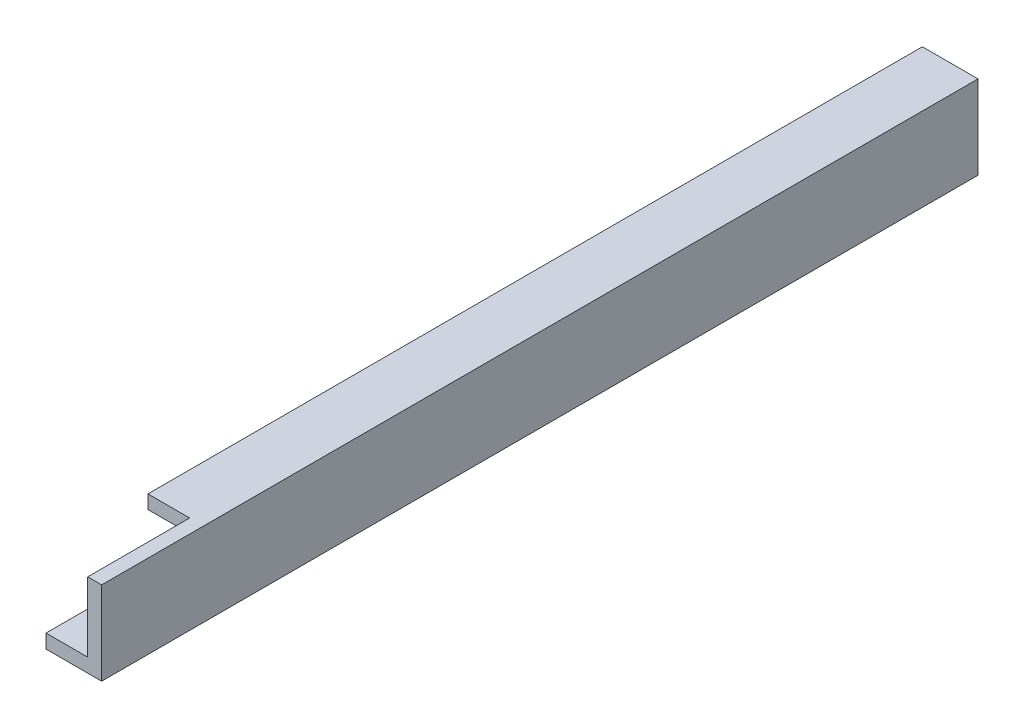
SolidWorks part; units mm, degrees
ref_plane "Front Plane" through (0, 0, 0) normal (0, 0, 1) x (1, 0, 0)
ref_plane "Top Plane" through (0, 0, 0) normal (0, 1, 0) x (1, 0, 0)
ref_plane "Right Plane" through (0, 0, 0) normal (1, 0, 0) x (0, 0, -1)
sketch "Sketch2" plane through (0, 0, 0) normal (0, 1, 0) x (1, 0, 0)
  line L1 (0, 0) -> (25.4, 0)
  line L2 (0, 0) -> (0, 400.05)
  line L3 (0, 400.05) -> (25.4, 400.05)
  line L4 (25.4, 0) -> (25.4, 400.05)
  dimension "D1" = 25.4
  dimension "D2" = 400.05
extrude "Boss-Extrude1" add sketch "Sketch2" along normal blind 6.35
sketch "Sketch4" plane through (0, 6.35, 0) normal (0, 1, 0) x (1, 0, 0)
  line L0 (25.4, 400.05) -> (0, 400.05) construction
  line L1 (19.05, 400.05) -> (25.4, 400.05)
  line L2 (19.05, 400.05) -> (19.05, 0)
  line L3 (19.05, 0) -> (25.4, 0)
  line L4 (25.4, 400.05) -> (25.4, 0)
  line L5 (25.4, 0) -> (25.4, 400.05) construction
  dimension "D1" = 6.35
extrude "Boss-Extrude2" add sketch "Sketch4" along normal blind 31.75
sketch "Sketch10" plane through (19.05, 0, 0) normal (-1, 0, 0) x (0, 0, 1)
  line L0 (-400.05, 38.1) -> (-400.05, 6.35) construction
  line L1 (-393.7, 6.4981) -> (-400.05, 6.4981)
  line L2 (-393.7, 6.4981) -> (-393.7, 31.8981)
  line L3 (-393.7, 31.8981) -> (-400.05, 31.8981)
  line L4 (-400.05, 6.4981) -> (-400.05, 31.8981)
  dimension "D1" = 6.35
  dimension "D2" = 25.4
extrude "Boss-Extrude6" add sketch "Sketch10" along normal blind 19.05
sketch "Sketch12" plane through (0, 0, -393.7) normal (0, 0, 1) x (1, 0, 0)
  line L0 (0, 19.1981) -> (19.05, 19.1981) construction
  line L1 (0, 6.4981) -> (0, 31.8981) construction
  line L2 (19.05, 6.4981) -> (19.05, 31.8981) construction
  line L3 (12.7, 6.4981) -> (12.7, 31.8981) construction
  line L4 (0, 6.4981) -> (19.05, 6.4981) construction
  line L5 (0, 31.8981) -> (19.05, 31.8981) construction
  circle A0 centre (12.7, 19.1981) radius 4.572
  dimension "D1" = 6.35
extrude "Cut-Extrude3" cut sketch "Sketch12" against normal blind 19.05
sketch "Sketch14" plane through (19.05, 0, 0) normal (-1, 0, 0) x (0, 0, 1)
  line L0 (-400.05, 6.35) -> (0, 6.35) construction
  line L1 (-260.35, 6.35) -> (-266.7, 6.35)
  line L2 (-260.35, 6.35) -> (-260.35, 31.75)
  line L3 (-260.35, 31.75) -> (-266.7, 31.75)
  line L4 (-266.7, 6.35) -> (-266.7, 31.75)
  dimension "D1" = 6.35
  dimension "D2" = 25.4
  dimension "D3" = 127
extrude "Boss-Extrude7" add sketch "Sketch14" along normal blind 19.05
sketch "Sketch15" plane through (0, 0, -260.35) normal (0, 0, 1) x (1, 0, 0)
  line L0 (0, 19.05) -> (19.05, 19.05) construction
  line L1 (0, 6.35) -> (0, 31.75) construction
  line L2 (19.05, 6.35) -> (19.05, 31.75) construction
  line L3 (12.7, 31.75) -> (12.7, 6.35) construction
  line L4 (0, 31.75) -> (19.05, 31.75) construction
  line L5 (0, 6.35) -> (19.05, 6.35) construction
  circle A0 centre (12.7, 19.05) radius 4.572
  dimension "D1" = 6.35
extrude "Cut-Extrude4" cut sketch "Sketch15" against normal blind 19.05
sketch "Sketch16" plane through (19.05, 0, 0) normal (-1, 0, 0) x (0, 0, 1)
  line L0 (-400.05, 38.1) -> (0, 38.1) construction
  line L1 (-400.05, 31.8981) -> (-46.5317, 31.8981)
  line L2 (-400.05, 31.8981) -> (-400.05, 38.1)
  line L3 (-400.05, 38.1) -> (-46.5317, 38.1)
  line L4 (-46.5317, 31.8981) -> (-46.5317, 38.1)
extrude "Boss-Extrude8" add sketch "Sketch16" along normal blind 19.05
